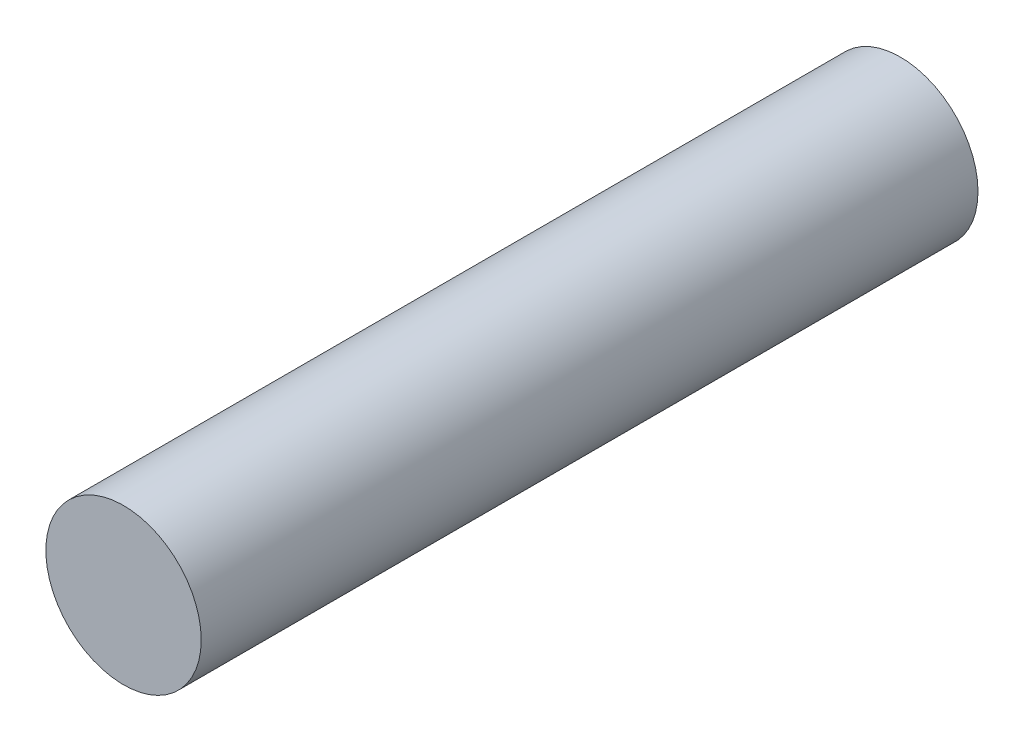
SolidWorks part; units mm, degrees
ref_plane "Plan de face" through (0, 0, 0) normal (0, 0, 1) x (1, 0, 0)
ref_plane "Plan de dessus" through (0, 0, 0) normal (0, 1, 0) x (1, 0, 0)
ref_plane "Plan de droite" through (0, 0, 0) normal (1, 0, 0) x (0, 0, -1)
sketch "Esquisse1" plane through (0, 0, 0) normal (0, 0, 1) x (1, 0, 0)
  circle A0 centre (0, 0) radius 3
  dimension "D1" = 6
extrude "Boss.-Extru.1" add sketch "Esquisse1" along normal blind 30 contours A0
